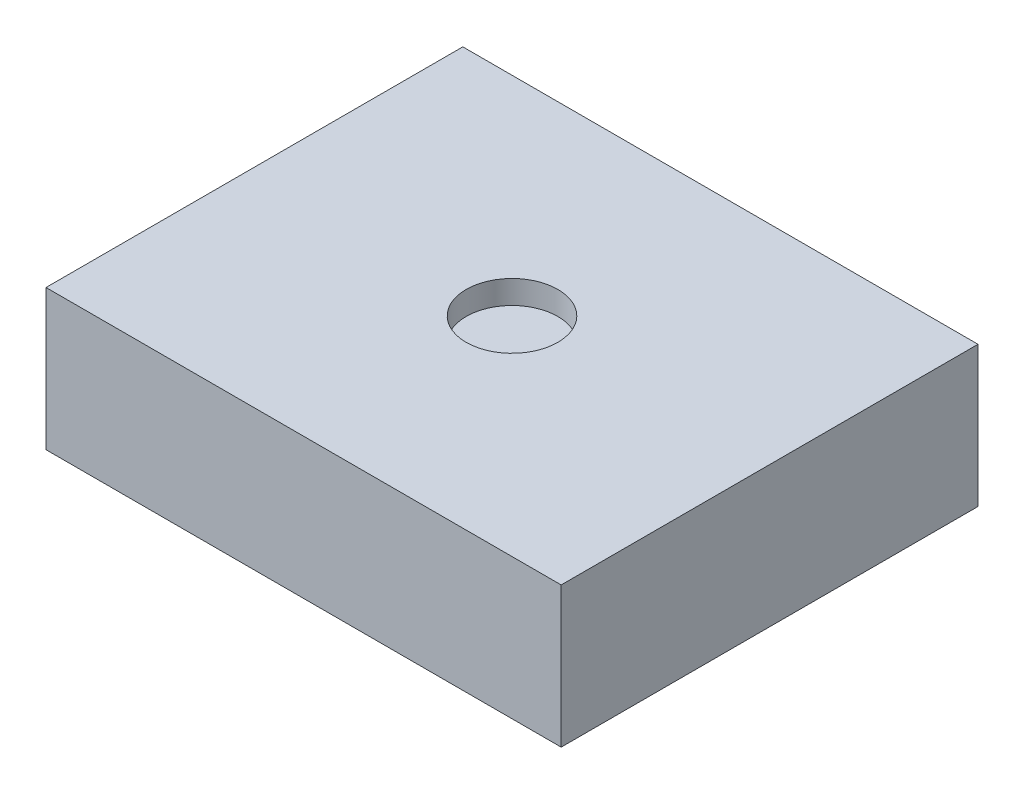
SolidWorks part; units mm, degrees
ref_plane "Front Plane" through (0, 0, 0) normal (0, 0, 1) x (1, 0, 0)
ref_plane "Top Plane" through (0, 0, 0) normal (0, 1, 0) x (1, 0, 0)
ref_plane "Right Plane" through (0, 0, 0) normal (1, 0, 0) x (0, 0, -1)
sketch "Sketch1" plane through (0, 0, 0) normal (0, 1, 0) x (1, 0, 0)
  line L1 (-13.97, -11.303) -> (13.97, -11.303)
  line L2 (-13.97, -11.303) -> (-13.97, 11.303)
  line L3 (-13.97, 11.303) -> (13.97, 11.303)
  line L4 (13.97, -11.303) -> (13.97, 11.303)
  line L5 (-13.97, -11.303) -> (13.97, 11.303) construction
  line L6 (-13.97, 11.303) -> (13.97, -11.303) construction
  point P0 (0, 0)
  dimension "D1" = 27.94
  dimension "D2" = 22.606
extrude "Boss-Extrude1" add sketch "Sketch1" along normal blind 7.62
sketch "Sketch2" plane through (0, 7.62, 0) normal (0, 1, 0) x (1, 0, 0)
  circle A0 centre (0, 0) radius 2.4863
  dimension "D1" = 4.9726
extrude "Cut-Extrude1" cut sketch "Sketch2" against normal blind 1.27
